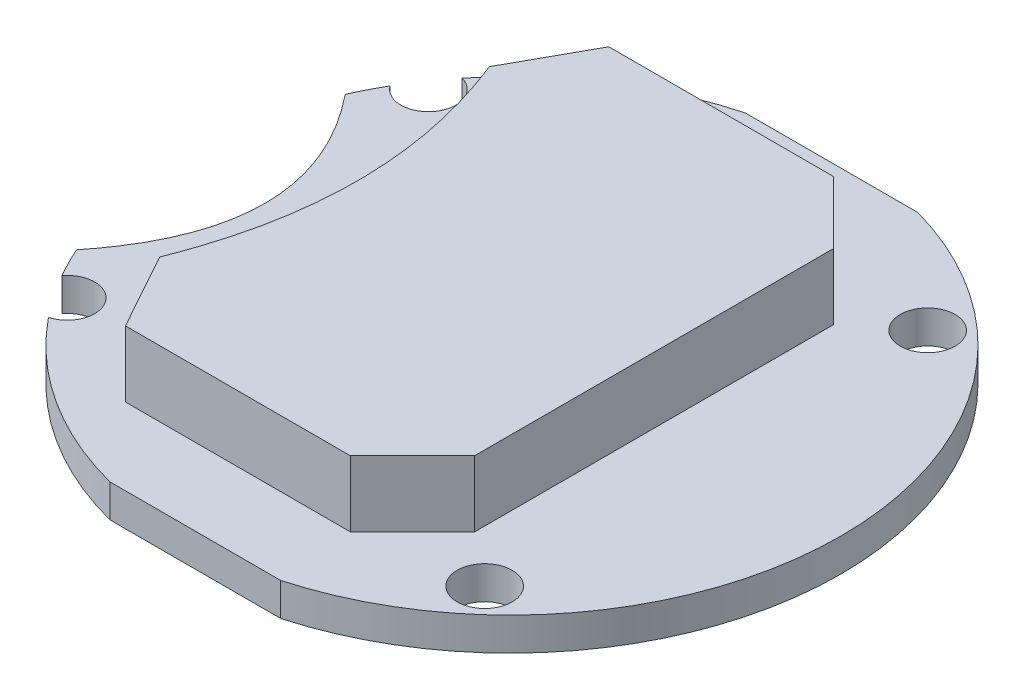
SolidWorks part; units mm, degrees
ref_plane "Спереди" through (0, 0, 0) normal (0, 0, 1) x (1, 0, 0)
ref_plane "Сверху" through (0, 0, 0) normal (0, 1, 0) x (1, 0, 0)
ref_plane "Справа" through (0, 0, 0) normal (1, 0, 0) x (0, 0, -1)
sketch "Эскиз1" plane through (0, 0, 0) normal (0, 1, 0) x (1, 0, 0)
  line L0 (-5, 14.5) -> (5, 14.5)
  line L1 (0, 15.6135) -> (0, -10.4601) construction
  line L2 (-31.7501, 0) -> (41.8405, 0) construction
  line L3 (-5, -14.5) -> (5, -14.5)
  line L4 (5, 9.6718) -> (5, -24.8067) construction
  line L5 (-5, 9.6718) -> (-5, -24.8067) construction
  line L6 (-13, 18.824) -> (-13, -24.3564)
  line L7 (-13, 6.5) -> (-7.4414, 0) construction
  line L8 (-7.4414, 0) -> (-13, -6.5) construction
  line L9 (-13, -6.5) -> (-13.5225, -7.5821) construction
  line L10 (-13.5225, -7.5821) -> (-13, -9.0189) construction
  line L11 (-13, 6.5) -> (-13.5225, 7.5821) construction
  line L12 (-13.5225, 7.5821) -> (-13, 9.0189) construction
  arc A0 (5, 14.5) -> (5, -14.5) centre (0.9404, 0) cw
  arc A3 (-5, 14.5) -> (-13, 9.0189) centre (-0.9367, -0.0094) ccw
  arc A4 (-5, -14.5) -> (-13, -9.0189) centre (-0.9367, 0.0094) cw
  spline S0 degree 2 poles (-13, 6.5) (-7.4414, 0) (-13, -6.5) knots 0 0 0 1 1 1
  spline S1 degree 2 poles (-13, -6.5) (-13.5225, -7.5821) (-13, -9.0189) knots 0 0 0 1 1 1
  spline S2 degree 2 poles (-13, 6.5) (-13.5225, 7.5821) (-13, 9.0189) knots 0 0 0 1 1 1
  point P7 (0, 14.5)
  point P11 (16, 0)
  point P13 (16, 0)
  point P17 (-16, 0)
  dimension "D1" = 10
  dimension "D2" = 29
  dimension "D3" = 11
  dimension "D4" = 11
  dimension "D5" = 8
  dimension "D6" = 6.5
  dimension "D7" = 6.5
extrude "Бобышка-Вытянуть1" add sketch "Эскиз1" along normal blind 1.5 contours L6 S0 A4 L3 A0 L0 A3
sketch "Эскиз3" plane through (0, 1.5, 0) normal (0, 1, 0) x (1, 0, 0)
  line L0 (4.669, -11) -> (7.4974, -8.1716)
  line L5 (-7.5026, -11) -> (7.501, 10.9976) construction
  line L6 (-7.4968, 11.0015) -> (7.4974, -11.0024) construction
  line L7 (-16.9863, 0) -> (25.6975, 0) construction
  line L8 (4.669, 11) -> (7.4974, 8.1716)
  line L10 (7.4974, 8.1716) -> (7.4974, -8.1716)
  line L12 (-7.5026, -7.5) -> (-5.5661, -11)
  line L13 (-7.5026, 7.5) -> (-5.5661, 11)
  line L14 (-5.5661, 11) -> (4.669, 11)
  line L15 (-5.5661, -11) -> (4.669, -11)
  line L17 (-7.5026, 7.5) -> (-4.5026, 0) construction
  line L18 (-4.5026, 0) -> (-7.5026, -7.5) construction
  spline S0 degree 2 poles (-7.5026, 7.5) (-4.5026, 0) (-7.5026, -7.5) knots 0 0 0 1 1 1
  point P0 (0, 0)
  point P12 (-7.5026, -7.5)
  point P17 (-6.0026, 0)
  dimension "D1" = 22
  dimension "D2" = 15
  dimension "D3" = 3.5
  dimension "D4" = 4
  dimension "D5" = 4
extrude "Бобышка-Вытянуть2" add sketch "Эскиз3" along normal blind 3
sketch "Эскиз5" plane through (0, 1.5, 0) normal (0, 1, 0) x (1, 0, 0)
  line L0 (-18.9148, 0) -> (21.4157, 0) construction
  circle A0 centre (9.8631, 10.081) radius 1.25
  circle A1 centre (-10.9978, 8.2188) radius 1.25
  circle A2 centre (9.8631, -10.081) radius 1.25
  circle A3 centre (-10.9978, -8.2188) radius 1.25
  dimension "D1" = 2.5
extrude "Вырез-Вытянуть2" cut sketch "Эскиз5" against normal through all
sketch "Эскиз7" plane through (0, 1.5, 0) normal (0, 1, 0) x (1, 0, 0)
  line L0 (-13, 9.0189) -> (-13, 6.5) construction
  line L1 (-13, -6.5) -> (-13, -9.0189) construction
  line L2 (-13, 9.0189) -> (-13, 6.5)
  line L3 (-13, -6.5) -> (-13, -9.0189)
  line L6 (-13, 6.5) -> (-12.7156, 6.0776)
  line L7 (-5, 14.5) -> (-2.8426, 14.5)
  line L8 (-2.7639, -14.5) -> (-5, -14.5)
  line L9 (-13, -6.5) -> (-12.6955, -6.0737)
  arc A1 (5, -14.5) -> (5, 14.5) centre (0.9404, 0) ccw construction
  arc A2 (-5, 14.5) -> (-13, 9.0189) centre (-0.9367, -0.0094) ccw construction
  arc A3 (-5, 14.5) -> (-13, 9.0189) centre (-0.9367, -0.0094) ccw
  arc A4 (-13, -9.0189) -> (-5, -14.5) centre (-0.9367, 0.0094) ccw construction
  arc A5 (-13, -9.0189) -> (-5, -14.5) centre (-0.9367, 0.0094) ccw
  arc A6 (-2.8426, 14.5) -> (-12.7156, 6.0776) centre (0.998, 0) ccw
  arc A7 (-12.6955, -6.0737) -> (-2.7639, -14.5) centre (0.998, 0) ccw
  point P3 (15.998, 0)
  point P4 (15.998, 0)
  point P15 (-2.8426, 14.5)
  point P17 (-12.7156, 6.0776)
  point P19 (-2.7639, -14.5)
  point P24 (-12.6955, -6.0737)
extrude "Вырез-Вытянуть3" cut sketch "Эскиз7" against normal through all
